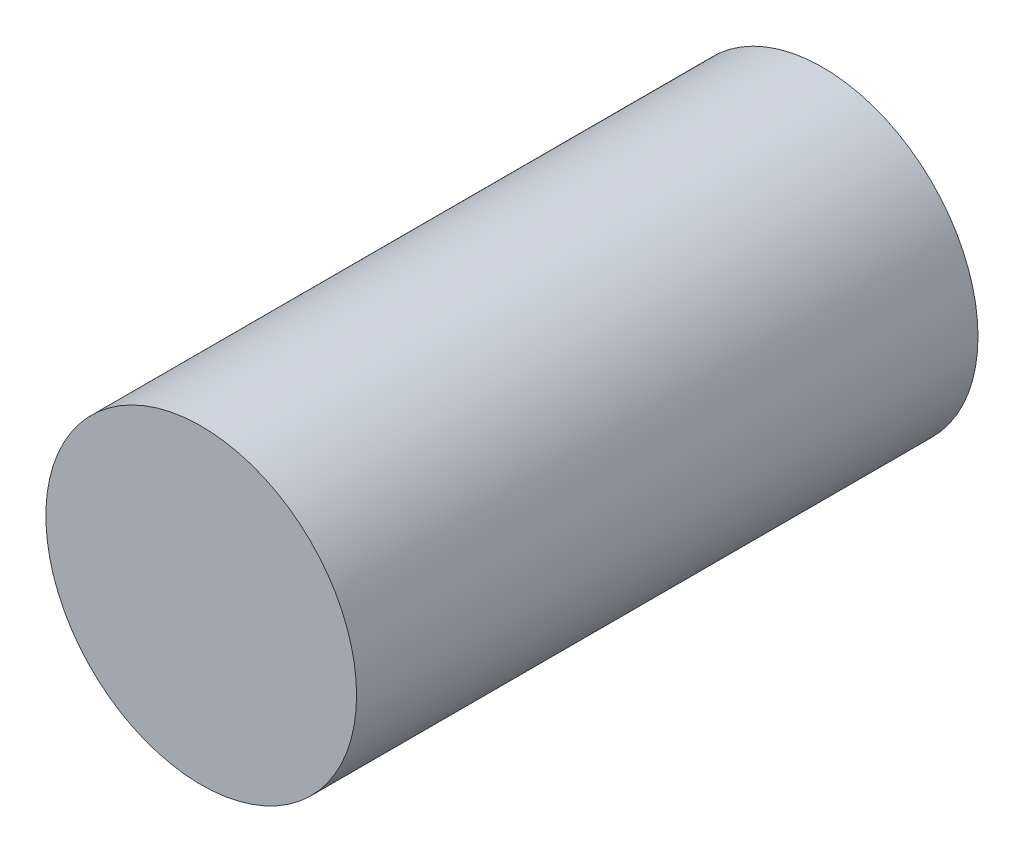
SolidWorks part; units mm, degrees
ref_plane "Front Plane" through (0, 0, 0) normal (0, 0, 1) x (1, 0, 0)
ref_plane "Top Plane" through (0, 0, 0) normal (0, 1, 0) x (1, 0, 0)
ref_plane "Right Plane" through (0, 0, 0) normal (1, 0, 0) x (0, 0, -1)
sketch "Sketch1" plane through (0, 0, 0) normal (0, 0, 1) x (1, 0, 0)
  circle A0 centre (0, 0) radius 5
  dimension "D1" = 10
extrude "Boss-Extrude1" add sketch "Sketch1" along normal blind 20
